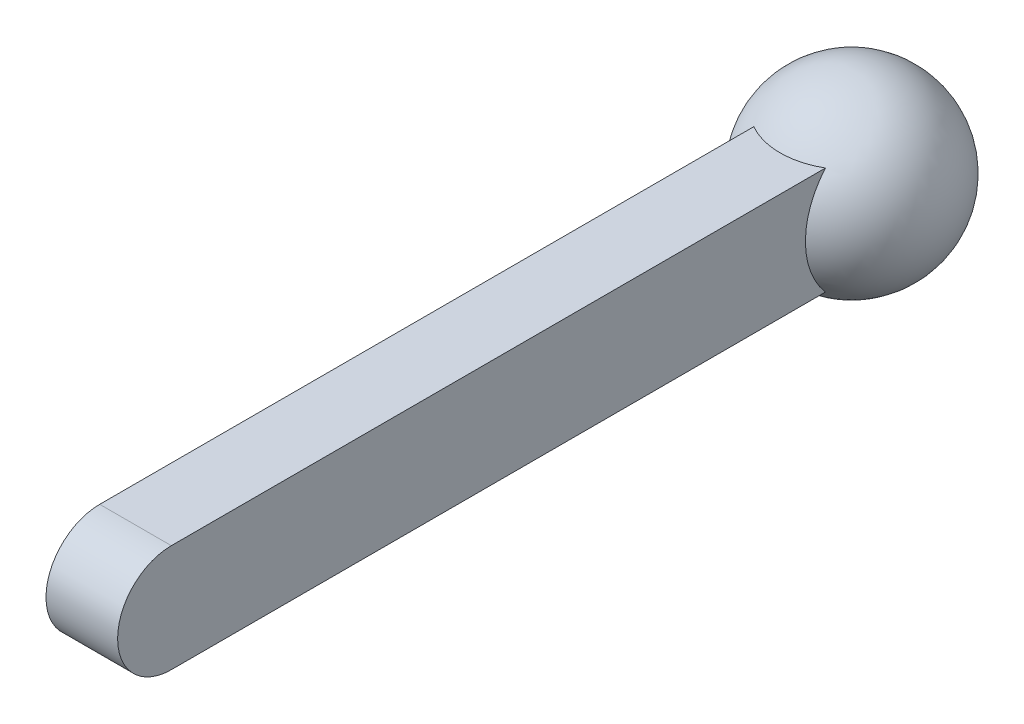
SolidWorks part; units mm, degrees
ref_plane "前视基准面" through (0, 0, 0) normal (0, 0, 1) x (1, 0, 0)
ref_plane "上视基准面" through (0, 0, 0) normal (0, 1, 0) x (1, 0, 0)
ref_plane "右视基准面" through (0, 0, 0) normal (1, 0, 0) x (0, 0, -1)
sketch "草图1" plane through (0, 0, 0) normal (1, 0, 0) x (0, 0, -1)
  line L1 (0, 15) -> (200, 15)
  line L2 (0, -15) -> (200, -15)
  arc A0 (0, 15) -> (0, -15) centre (0, 0) ccw
  arc A1 (200, -15) -> (200, 15) centre (200, 0) ccw
extrude "凸台-拉伸1" add sketch "草图1" along normal mid plane 20
sketch "草图2" plane through (0, 0, 0) normal (1, 0, 0) x (0, 0, -1)
  line L1 (200, 25) -> (200, -25)
  arc A1 (200, -25) -> (200, 25) centre (200, 0) ccw
revolve "旋转1" add sketch "草图2" angle 360 about L1
